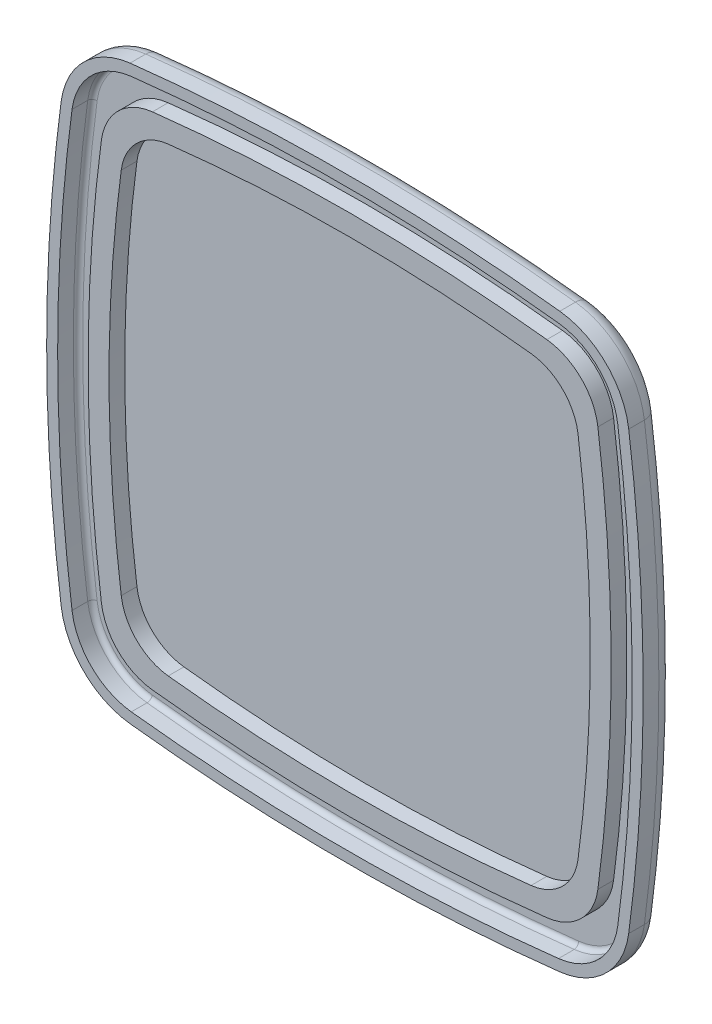
SolidWorks part; units mm, degrees
ref_plane "Ön Düzlem" through (0, 0, 0) normal (0, 0, 1) x (1, 0, 0)
ref_plane "Üst Düzlem" through (0, 0, 0) normal (0, 1, 0) x (1, 0, 0)
ref_plane "Sağ Düzlem" through (0, 0, 0) normal (1, 0, 0) x (0, 0, -1)
sketch "Çizim1" plane through (0, 0, 0) normal (0, 0, 1) x (1, 0, 0)
  line L1 (-19, -19) -> (19, -19)
  line L2 (-19, -19) -> (-19, 19)
  line L3 (-19, 19) -> (19, 19)
  line L4 (19, -19) -> (19, 19)
  line L5 (-19, -19) -> (19, 19) construction
  line L6 (-19, 19) -> (19, -19) construction
  point P0 (0, 0)
  dimension "D1" = 38
  dimension "D2" = 38
extrude "Yükseklik-Ekstrüzyon1" add sketch "Çizim1" along normal mid plane 2 contours L3 L4 L1 L2
sketch "Çizim2" plane through (0, 0, 1) normal (0, 0, 1) x (1, 0, 0)
  line L0 (-19, 17.5) -> (19, 17.5) construction
  line L1 (-19, -19) -> (-19, 19) construction
  line L2 (19, -19) -> (19, 19) construction
  line L3 (-19, 19) -> (19, 19) construction
  line L4 (0, 0) -> (12.6557, 0) construction
  line L5 (-19, 19) -> (19, 19)
  line L6 (19, 19) -> (19, 17.5)
  line L7 (-19, 19) -> (-19, 17.5)
  line L8 (-19, -17.5) -> (19, -17.5) construction
  line L9 (-19, -19) -> (-19, -17.5)
  line L10 (19, -19) -> (19, -17.5)
  line L11 (-19, -19) -> (19, -19)
  arc A0 (-19, 17.5) -> (19, 17.5) centre (0, -102.0833) cw
  arc A1 (-19, -17.5) -> (19, -17.5) centre (0, 102.0833) ccw
  line M4 (-19, 19) -> (-19, -19)
  line M5 (-19, -19) -> (19, -19)
  line M6 (19, -19) -> (19, 19)
  line M7 (19, 19) -> (-19, 19)
  dimension "D1" = 1.5
extrude "Kes-Ekstrüzyon1" cut sketch "Çizim2" against normal through all contours A0 M7 M6 | A0 L5 M4 | A1 M4 M5 | A1 L11 M6
sketch "Çizim3" plane through (0, 0, 1) normal (0, 0, 1) x (1, 0, 0)
  line L0 (17.5, 17.7287) -> (17.5, -17.7287) construction
  line L1 (19, -17.5) -> (19, 17.5) construction
  line L2 (19, 17.5) -> (19, -17.5)
  line L3 (0, 0) -> (0, -12.7146) construction
  line L4 (-17.5, 17.7287) -> (-17.5, -17.7287) construction
  line L5 (-19, 17.5) -> (-19, -17.5)
  arc A0 (19, 17.5) -> (-19, 17.5) centre (0, -102.0833) ccw construction
  arc A1 (-19, -17.5) -> (19, -17.5) centre (0, 102.0833) ccw construction
  arc A2 (17.5, 17.7287) -> (17.5, -17.7287) centre (-86.5189, 0) cw
  arc A3 (17.5, -17.7287) -> (19, -17.5) centre (0, 102.0833) ccw
  arc A4 (19, 17.5) -> (17.5, 17.7287) centre (0, -102.0833) ccw
  arc A5 (-19, 17.5) -> (-17.5, 17.7287) centre (0, -102.0833) cw
  arc A6 (-17.5, -17.7287) -> (-19, -17.5) centre (0, 102.0833) cw
  arc A7 (-17.5, 17.7287) -> (-17.5, -17.7287) centre (86.5189, 0) ccw
  arc M3 (-19, -17.5) -> (19, -17.5) centre (0, 102.0833) ccw
  line M4 (19, -17.5) -> (19, 17.5)
  arc M5 (19, 17.5) -> (-19, 17.5) centre (0, -102.0833) ccw
  line M6 (-19, 17.5) -> (-19, -17.5)
  dimension "D1" = 1.5
extrude "Kes-Ekstrüzyon2" cut sketch "Çizim3" against normal through all contours A2 L2 M5 | A2 M4 M3 | A7 L5 M3 | A7 M5 M6
fillet "Radyus1" radius 5 4 edges at (-17.5, -17.7287, 0) (17.5, -17.7287, 0) (-17.5, 17.7287, 0) (17.5, 17.7287, 0)
fillet "Radyus2" radius 1 8 edges at (16.6239, 16.8249, -1) (0, 19, -1) (-16.6239, 16.8249, -1) (-19, 0, -1) (-16.6239, -16.8249, -1) (0, -19, -1) (16.6239, -16.8249, -1) (19, 0, -1)
shell "İç Boşaltma1" thickness 0.7
sketch "Çizim10" plane through (0, 0, -0.3) normal (0, 0, 1) x (1, 0, 0)
  arc A21 (12.5637, 15.9476) -> (-12.5637, 15.9476) centre (0, -94.4838) ccw
  arc A22 (-12.5637, 15.9476) -> (-15.8151, 12.7573) centre (-12.1452, 12.2691) ccw
  arc A23 (-15.8151, 12.7573) -> (-15.8151, -12.7573) centre (80.0781, 0) ccw
  arc A24 (-15.8151, -12.7573) -> (-12.5637, -15.9476) centre (-12.1452, -12.2691) ccw
  arc A25 (-12.5637, -15.9476) -> (12.5637, -15.9476) centre (0, 94.4838) ccw
  arc A26 (12.5637, -15.9476) -> (15.8151, -12.7573) centre (12.1452, -12.2691) ccw
  arc A27 (15.8151, -12.7573) -> (15.8151, 12.7573) centre (-80.0781, 0) ccw
  arc A28 (15.8151, 12.7573) -> (12.5637, 15.9476) centre (12.1452, 12.2691) ccw
extrude "Yükseklik-Ekstrüzyon10" add sketch "Çizim10" along normal blind 1 separate body
sketch "Çizim15" plane through (0, 0, 0.7) normal (0, 0, 1) x (1, 0, 0)
  arc A16 (14.5499, 11.7368) -> (11.5586, 14.6718) centre (11.1736, 11.2876) ccw
  arc A17 (11.5586, 14.6718) -> (-11.5586, 14.6718) centre (0, -86.9251) ccw
  arc A18 (-11.5586, 14.6718) -> (-14.5499, 11.7368) centre (-11.1736, 11.2876) ccw
  arc A19 (-14.5499, 11.7368) -> (-14.5499, -11.7368) centre (73.6718, 0) ccw
  arc A20 (-14.5499, -11.7368) -> (-11.5586, -14.6718) centre (-11.1736, -11.2876) ccw
  arc A21 (-11.5586, -14.6718) -> (11.5586, -14.6718) centre (0, 86.9251) ccw
  arc A22 (11.5586, -14.6718) -> (14.5499, -11.7368) centre (11.1736, -11.2876) ccw
  arc A23 (14.5499, -11.7368) -> (14.5499, 11.7368) centre (-73.6718, 0) ccw
extrude "Kes-Ekstrüzyon7" cut sketch "Çizim15" against normal blind 1
